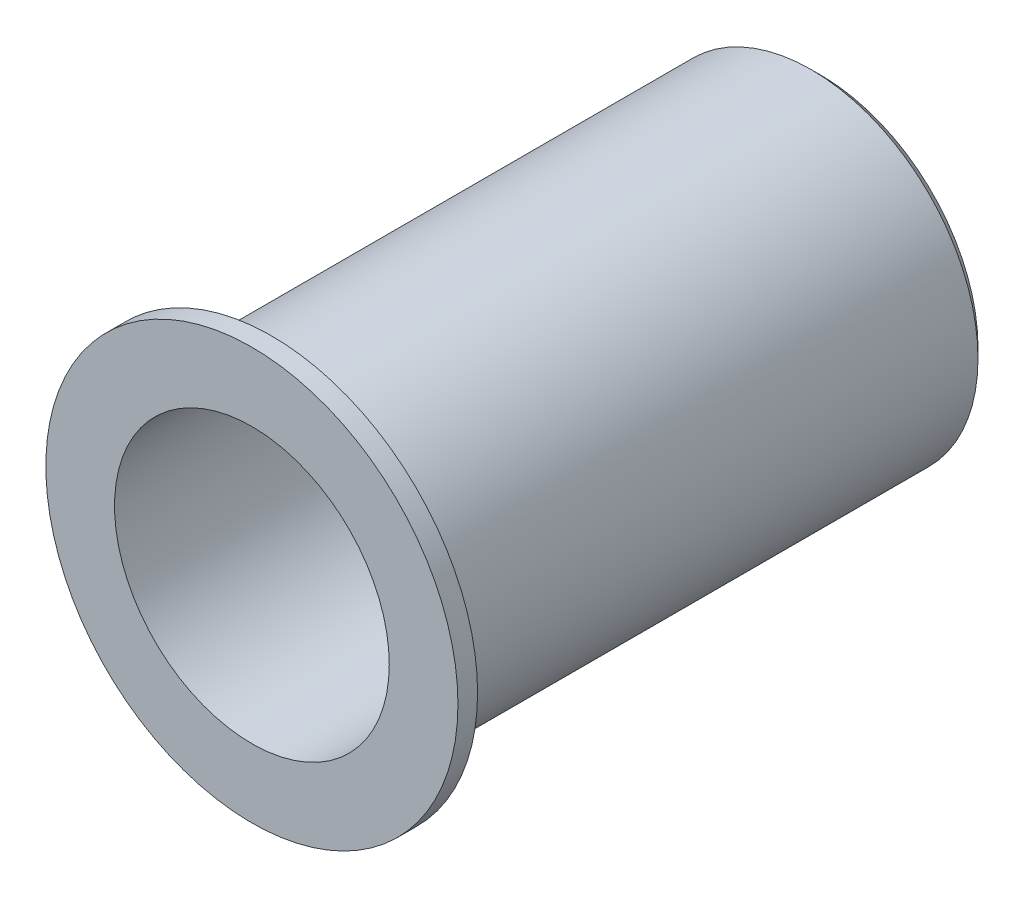
SolidWorks part; units mm, degrees
ref_plane "前视基准面" through (0, 0, 0) normal (0, 0, 1) x (1, 0, 0)
ref_plane "上视基准面" through (0, 0, 0) normal (0, 1, 0) x (1, 0, 0)
ref_plane "右视基准面" through (0, 0, 0) normal (1, 0, 0) x (0, 0, -1)
sketch "草图1" plane through (0, 0, 0) normal (0, 0, 1) x (1, 0, 0)
  circle A0 centre (0, 0) radius 8.5
  dimension "D1" = 17
extrude "凸台-拉伸1" add sketch "草图1" along normal blind 28
sketch "草图2" plane through (0, 0, 28) normal (0, 0, 1) x (1, 0, 0)
  circle A0 centre (0, 0) radius 7
extrude "切除-拉伸3" cut sketch "草图2" against normal blind 23
sketch "草图3" plane through (0, 0, 0) normal (0, 0, -1) x (-1, 0, 0)
  circle A0 centre (0, 0) radius 7 construction
  circle A1 centre (0, 0) radius 5
  circle A3 centre (0, 0) radius 7
  point P2 (0, 5)
  point P7 (4.3301, -2.5)
  point P8 (-4.3301, -2.5)
  point P9 (0, 0)
  dimension "D1" = 10
  dimension "D2" = 3
hole_wizard "M4 螺纹孔1" positions "草图8" profile "草图9" tap size "M4" standard "GB" end condition through all
sketch "草图8" plane through (0, 0, 0) normal (0, 0, -1) x (-1, 0, 0)
  point P0 (0, 5)
  point P3 (0, 0)
  point P6 (-4.3301, -2.5)
  point P9 (4.3301, -2.5)
sketch "草图9" plane through (0, 5, 0) normal (1, 0, 0) x (0, 1, 0)
  line L0 (0, 0) -> (0, 28)
  line L1 (0, 28) -> (1.65, 28)
  line L2 (1.65, 28) -> (1.65, 0)
  line L5 (1.65, 0) -> (0, 0)
  line L11 (0, -6.35) -> (0, 107.95) construction
  dimension "通孔螺纹孔钻头直径" = 3.3
  dimension "通孔螺纹孔钻头深度" = 28
cosmetic thread "孔螺蚊线5" parameters "D2"=4
cosmetic thread "孔螺蚊线6" parameters "D2"=4
cosmetic thread "孔螺蚊线7" parameters "D2"=4
cosmetic thread "孔螺蚊线8" parameters "D2"=4
sketch "草图10" plane through (0, 0, 28) normal (0, 0, 1) x (1, 0, 0)
  circle A0 centre (0, 0) radius 10.5
  circle A1 centre (0, 0) radius 8.5
  circle A2 centre (0, 0) radius 8.5
  circle A3 centre (0, 0) radius 7 construction
  circle A4 centre (0, 0) radius 7
  circle M2 centre (0, 0) radius 7
  circle M3 centre (0, 0) radius 8.5
  dimension "D1" = 0
  dimension "D2" = 2
extrude "凸台-拉伸4" add sketch "草图10" along normal blind 1 contours A0 M3 | M3 M2
chamfer "倒角1" distance 0.5 angle 45 1 edges at (8.5, 0, 0)
